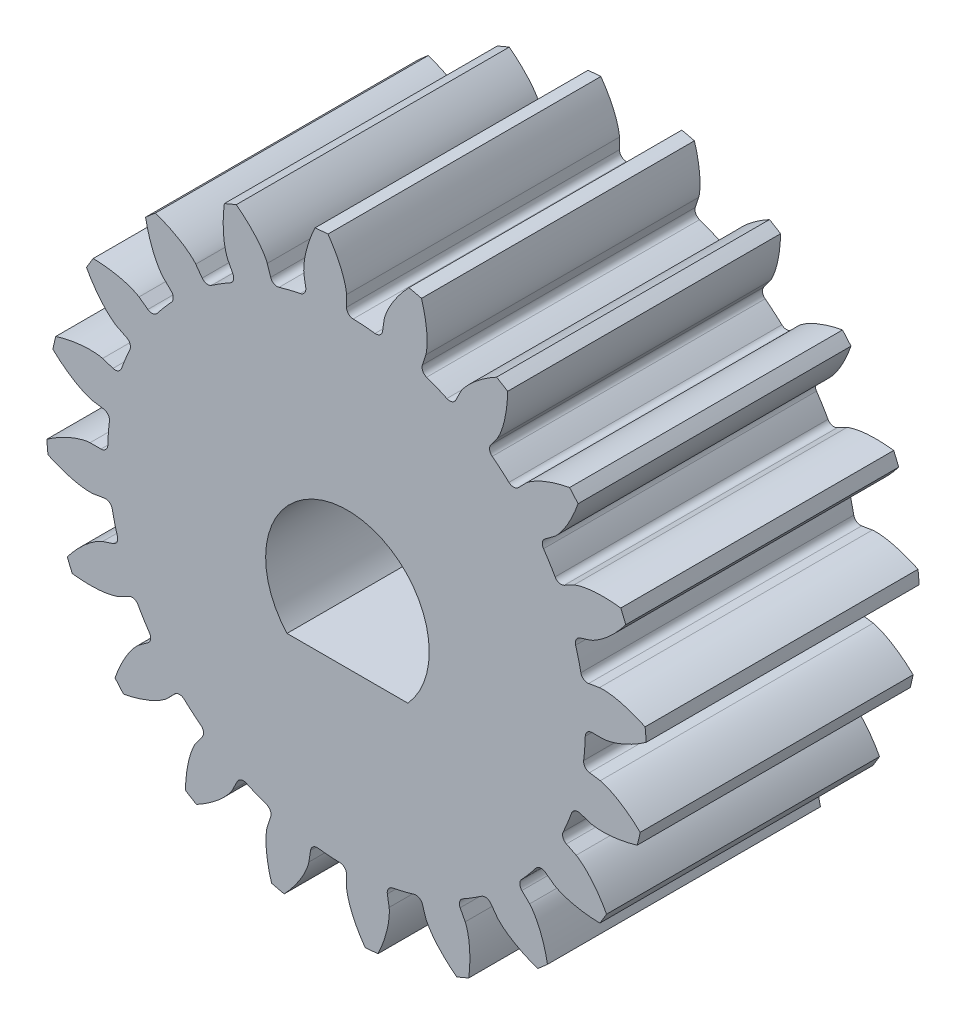
SolidWorks part; units mm, degrees
material "Acrilico (impatto medio-alto)"
ref_plane "Front Plane" through (0, 0, 0) normal (0, 0, 1) x (1, 0, 0)
ref_plane "Top Plane" through (0, 0, 0) normal (0, 1, 0) x (1, 0, 0)
ref_plane "Right Plane" through (0, 0, 0) normal (1, 0, 0) x (0, 0, -1)
sketch "Sketch1" plane through (0, 0, 0) normal (0, 0, 1) x (1, 0, 0)
  line L0 (4.6985, 0) -> (4.375, 0)
  line L1 (5.4809, 0.4584) -> (-5.4809, -0.4584)
  line L2 (0, 0) -> (4.9994, 0.0745) construction
  circle A0 centre (0, 0) radius 4.6985 construction
  circle A1 centre (0, 0) radius 5.5
  circle A2 centre (0, 0) radius 4.375
  circle A3 centre (0, 0) radius 5 construction
  spline S0 degree 4 poles (4.6985, 0) (4.7019, 0.0001) (4.7117, 0.0005) (4.73, 0.0022) (4.7599, 0.0063) (4.7977, 0.0133) (4.8462, 0.0246) (4.9027, 0.0405) (4.9642, 0.0609) (5.0303, 0.086) (5.0954, 0.1137) (5.1594, 0.1437) (5.2224, 0.1758) (5.2977, 0.2172) (5.3864, 0.2702) (5.4878, 0.3372) (5.5997, 0.4188) (5.7102, 0.508) (5.8161, 0.6006) (5.9193, 0.6994) (6.0166, 0.7988) (6.1136, 0.9071) (6.2011, 1.0098) (6.2943, 1.1303) (6.3682, 1.2291) (6.4603, 1.365) (6.5131, 1.4469) (6.573, 1.5445) (6.5986, 1.5888) (6.6144, 1.6161) knots 0 0 0 0 0 0.005377 0.015084 0.028532 0.04661 0.064855 0.092111 0.119476 0.146842 0.174209 0.201575 0.228941 0.256307 0.307035 0.361767 0.4165 0.471232 0.525964 0.580697 0.635429 0.690161 0.744894 0.799626 0.854358 0.909091 0.954545 1 1 1 1 1 construction
  spline S1 degree 4 poles (4.6985, 0) (4.7019, 0.0001) (4.7117, 0.0005) (4.73, 0.0022) (4.7599, 0.0063) (4.7977, 0.0133) (4.8462, 0.0246) (4.9027, 0.0405) (4.9642, 0.0609) (5.0303, 0.086) (5.0954, 0.1137) (5.1594, 0.1437) (5.2224, 0.1758) (5.2977, 0.2172) (5.3864, 0.2702) (5.4878, 0.3372) (5.5997, 0.4188) (5.7102, 0.508) (5.8161, 0.6006) (5.9193, 0.6994) (6.0166, 0.7988) (6.1136, 0.9071) (6.2011, 1.0098) (6.2943, 1.1303) (6.3682, 1.2291) (6.4403, 1.3356) (6.4748, 1.388) (6.4922, 1.415) knots 0 0 0 0 0 0.005377 0.015084 0.028532 0.04661 0.064855 0.092111 0.119476 0.146842 0.174209 0.201575 0.228941 0.256307 0.307035 0.361767 0.4165 0.471232 0.525964 0.580697 0.635429 0.690161 0.744894 0.799626 0.854358 0.909091 0.909091 0.909091 0.909091 0.909091
  dimension "D1" = 9.3969
  dimension "D2" = 11
  dimension "D3" = 8.75
  dimension "D5" = 10
  dimension "D4" = 3.927
extrude "Boss-Extrude3" add sketch "Sketch1" along normal blind 5 contours L1 A2 | A2 L1 | L0 S1 A1 L1 A2
mirror "Mirror2" about plane through (0, 0, 5) normal (0.0833, -0.9965, 0) of "Boss-Extrude3"
fillet "Fillet1" radius 0.125 2 edges at (4.3142, 0.7268, 2.5) (4.375, 0, 2.5)
pattern_circular "CirPattern8" count 20 over 360 about axis through (0, 0, 5) along (0, 0, -1) of "Boss-Extrude3", "Mirror2", "Fillet1"
sketch "Sketch3" plane through (0, 0, 5) normal (0, 0, 1) x (1, 0, 0)
  line L0 (40.9064, 174.787) -> (208.9064, 174.787) construction
  line L1 (-1.09, -1.2209) -> (1.1229, -1.2209)
  arc A0 (1.1229, -1.2209) -> (-1.09, -1.2209) centre (0.0164, -0.2106) ccw
  dimension "D1" = 2.2129
extrude "Cut-Extrude2" cut sketch "Sketch3" against normal through all
sketch "Schizzo2" plane through (0, 0, 0) normal (0, 0, -1) x (-1, 0, 0)
  line L0 (-2.0898, 0) -> (-2.8939, 0)
  line L1 (0, -2.0898) -> (0, -1.5898)
  line L2 (0, -2.8939) -> (0, -3.3939)
  line L3 (0, -2.0898) -> (0, -2.8939) construction
  line L4 (0, -2.8939) -> (0, -2.4918) construction
  line L5 (0, -2.4918) -> (-1.1735, -2.4918) construction
  line L6 (0, -1.5898) -> (-1.1735, -2.4918)
  line L7 (-1.1735, -2.4918) -> (0, -3.3939)
  arc A0 (0, -2.0898) -> (-2.0898, 0) centre (0, 0) ccw
  arc A1 (0, -2.8939) -> (-2.8939, 0) centre (0, 0) ccw
  dimension "D1" = 0.5
  dimension "D2" = 0.5
extrude "Taglio-Estrusione2" cut sketch "Schizzo2" against normal blind 0.3
equation "\"d\"= 10mm'Pitch diameter"
equation "\"N\"= 20'Number of teeth"
equation "\"bl\"= 0.1mm'Backlash"
equation "\"pa\"= 20gradi'Pressure angle (deg)"
equation "\"pc\"= ( 3.1415 * \"d\" ) / \"N\"\t'Circular pitch"
equation "\"m\"= \"d\" / \"N\"'module"
equation "\"P\"= \"N\" / \"d\"\t\t\t'Diametral pitch"
equation "\"a\"= 1/\"P\"\t\t\t'Addendum distance"
equation "\"b\"= 1.25 / \"P\"'Dedendum distance"
equation "\"rb\"= (\"d\"/2)*cos(\"pa\")\t\t'base circle radius"
equation "\"cp\"= 3.1415/\"P\"\t\t'Circular pitch"
equation "\"t\"= ( \"cp\" / 2 ) - \"bl\"'tooth tickness"
equation "\"c\"=\"b\"-\"a\"\t\t\t'Clearance"
equation "\"facewidth\"= 5mm'face width"
equation "\"rbd\"= \"rb\" * 2'base circle diameter"
equation "\"D1@Sketch1\"=\"rbd\""
equation "\"D2@Sketch1\"= \"d\" + (\"a\" * 2)"
equation "\"D3@Sketch1\" = \"ded\""
equation "\"D4@Sketch1\"= ((\"t\" /2) / (\"d\"/2)) * (180/3.1415)"
equation "\"D1@Boss-Extrude3\"=\"facewidth\""
equation "\"D1@Fillet1\"=\"c\""
equation "\"D1@CirPattern8\"=\"N\""
equation "\"D5@Sketch1\"=\"d\""
equation "\"ded1\"= \"d\" - 2 * ( ( ( \"d\" / 2 ) - \"rb\" ) + ( 0.5 * ( 1.25 / \"P\" ) ) )"
equation "\"ded2\"= \"d\" - ( \"b\" * 2 )"
equation "\"ded\"= IIF ( \"rb\" < ( \"ded2\" / 2 ) , \"ded1\" , \"ded2\" )"
equation "\"shaftdia\"= 4mm"
